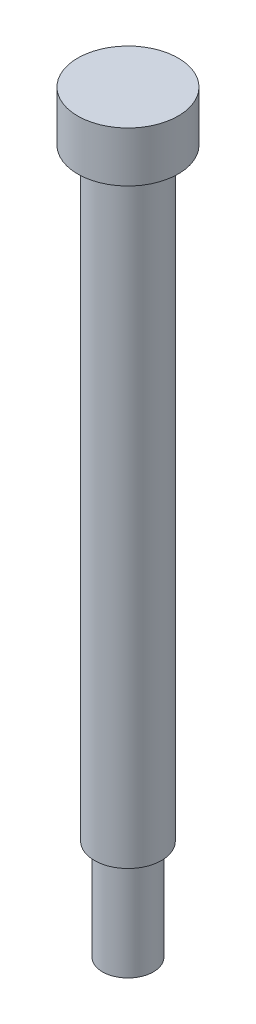
SolidWorks part; units mm, degrees
ref_plane "Front" through (0, 0, 0) normal (0, 0, 1) x (1, 0, 0)
ref_plane "Top" through (0, 0, 0) normal (0, 1, 0) x (1, 0, 0)
ref_plane "Right" through (0, 0, 0) normal (1, 0, 0) x (0, 0, -1)
sketch "profile" plane through (0, 0, 0) normal (0, 0, 1) x (1, 0, 0)
  line L0 (0, 24.8324) -> (0, -34.6109) construction
  line L1 (0, 4.7625) -> (4.7625, 4.7625)
  line L2 (4.7625, 4.7625) -> (4.7625, 0)
  line L3 (4.7625, 0) -> (3.175, 0)
  line L4 (3.175, 0) -> (3.175, -57.15)
  line L5 (3.175, -57.15) -> (2.413, -57.15)
  line L6 (2.413, -57.15) -> (2.413, -66.675)
  line L7 (2.413, -66.675) -> (0, -66.675)
  line L8 (0, -66.675) -> (0, 4.7625)
  dimension "head_diameter" = 9.525
  dimension "shoulder_diameter" = 6.35
  dimension "thread_diameter" = 4.826
  dimension "head_height" = 4.7625
  dimension "shoulder_length" = 57.15
  dimension "thread_length" = 9.525
revolve "Base-Revolve" add sketch "profile" angle 360 about L0
